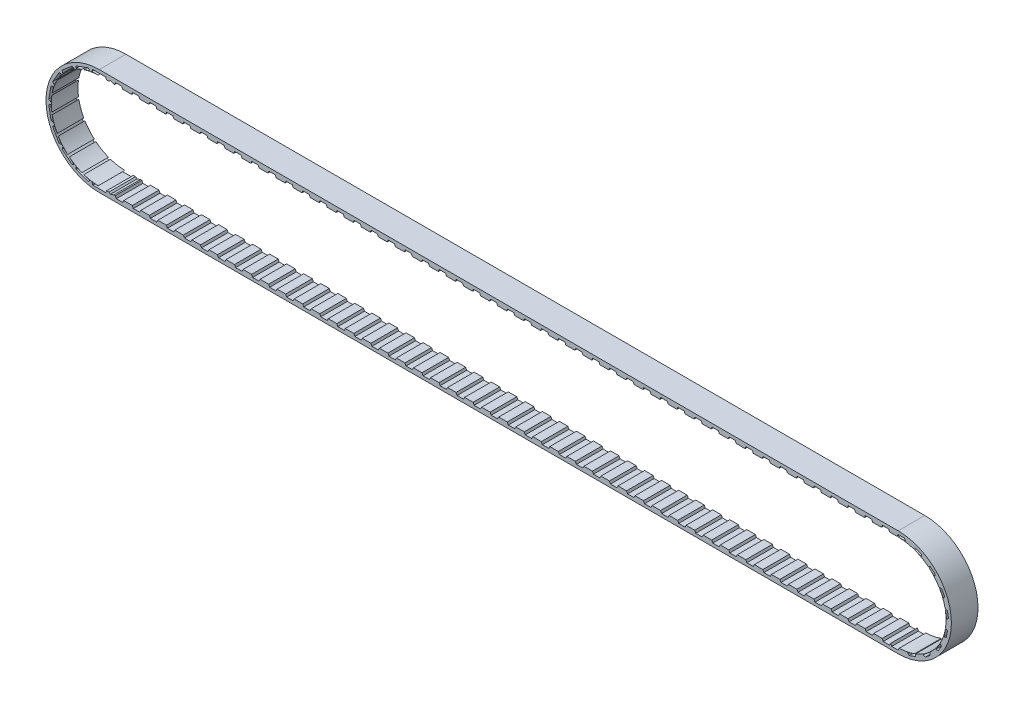
SolidWorks part; units mm, degrees
ref_plane "Front Plane" through (0, 0, 0) normal (0, 0, 1) x (1, 0, 0)
ref_plane "Top Plane" through (0, 0, 0) normal (0, 1, 0) x (1, 0, 0)
ref_plane "Right Plane" through (0, 0, 0) normal (1, 0, 0) x (0, 0, -1)
sketch "Sketch1" plane through (0, 0, 0) normal (0, 0, 1) x (1, 0, 0)
  line L1 (-95.25, 12.7) -> (95.25, 12.7)
  line L2 (-95.2554, 11.43) -> (95.2554, 11.43)
  line L3 (-95.25, -12.7) -> (95.25, -12.7)
  line L5 (-95.25, 12.7) -> (95.25, -12.7) construction
  line L6 (-95.25, -12.7) -> (95.25, 12.7) construction
  line L7 (-95.2554, -11.43) -> (95.2554, -11.43)
  line L9 (-95.2554, 11.43) -> (95.2554, -11.43) construction
  line L10 (-95.2554, -11.43) -> (95.2554, 11.43) construction
  arc A0 (-95.25, 12.7) -> (-95.25, -12.7) centre (-95.25, 0) ccw
  arc A1 (95.25, 12.7) -> (95.25, -12.7) centre (95.25, 0) cw
  arc A2 (-95.2554, 11.43) -> (-95.2554, -11.43) centre (-95.2554, 0) ccw
  arc A3 (95.2554, 11.43) -> (95.2554, -11.43) centre (95.2554, 0) cw
  point P0 (0, 0)
  point P8 (0, 0)
  dimension "D2" = 12.7
  dimension "D1" = 190.5
  dimension "D3" = 1.27
extrude "Boss-Extrude1" add sketch "Sketch1" against normal blind 6.35
sketch "Sketch2" plane through (0, 0, 0) normal (0, 0, 1) x (1, 0, 0)
  line L0 (-93.7314, -11.938) -> (-93.4774, -11.43)
  line L1 (-95.2554, -11.303) -> (-93.7314, -11.303)
  line L2 (-95.25, -12.7) -> (95.25, -12.7) construction
  line L3 (-95.2554, -11.938) -> (-93.7314, -11.938)
  line L4 (-95.2554, -11.303) -> (-95.5711, -11.303)
  line L5 (-95.2554, -11.43) -> (95.2554, -11.43) construction
  line L7 (-95.5094, -11.4272) -> (-95.2554, -11.938)
  line L8 (-95.5711, -11.303) -> (-95.5094, -11.4272)
  line L9 (-93.4774, -11.43) -> (-93.4139, -11.303)
  line L10 (-93.4139, -11.303) -> (-93.7314, -11.303)
  arc A0 (-95.2554, 11.43) -> (-95.2554, -11.43) centre (-95.2554, 0) ccw construction
  line M5 (95.2554, -11.43) -> (-95.2554, -11.43)
  arc M6 (-95.2554, -11.43) -> (-95.2554, 11.43) centre (-95.2554, 0) cw
  dimension "D2" = 1.524
  dimension "D4" = 0.635
  dimension "D5" = 0.762
extrude "Cut-Extrude1" cut sketch "Sketch2" against normal blind 8.89 contours L7 L3 L0 M6 M5
pattern_curve "CrvPattern1" of "Cut-Extrude1" parameters "D1"=48, "D3"=4.064, "D2"=1, "D4"=2.54
pattern_circular "CirPattern1" count 18 over 360 about axis through (-95.2554, 0, 0) along (0, 0, 1) of "Cut-Extrude1"
mirror "Mirror1" about plane through (0, 0, 0) normal (1, 0, 0) of "CirPattern1", "Cut-Extrude1"
mirror "Mirror2" about plane through (0, 0, 0) normal (0, 1, 0) of "CirPattern1", "Cut-Extrude1"
sketch "Sketch3" plane through (0, 0, 0) normal (0, 0, 1) x (1, 0, 0)
  line L0 (-91.6459, 11.303) -> (-89.6139, 11.303)
  line L1 (-89.6139, 11.303) -> (-89.8679, 11.938)
  line L2 (-89.8679, 11.938) -> (-91.3919, 11.938)
  line L3 (-91.3919, 11.938) -> (-91.6459, 11.303)
  line L4 (95.25, 12.7) -> (-95.25, 12.7) construction
  dimension "D1" = 2.032
  dimension "D2" = 0.635
  dimension "D3" = 0.762
  dimension "D4" = 1.524
extrude "Cut-Extrude2" cut sketch "Sketch3" against normal blind 8.89
pattern_linear "LPattern2" count 46 spacing 4.064 along (1, 0, 0) of "Cut-Extrude2"
